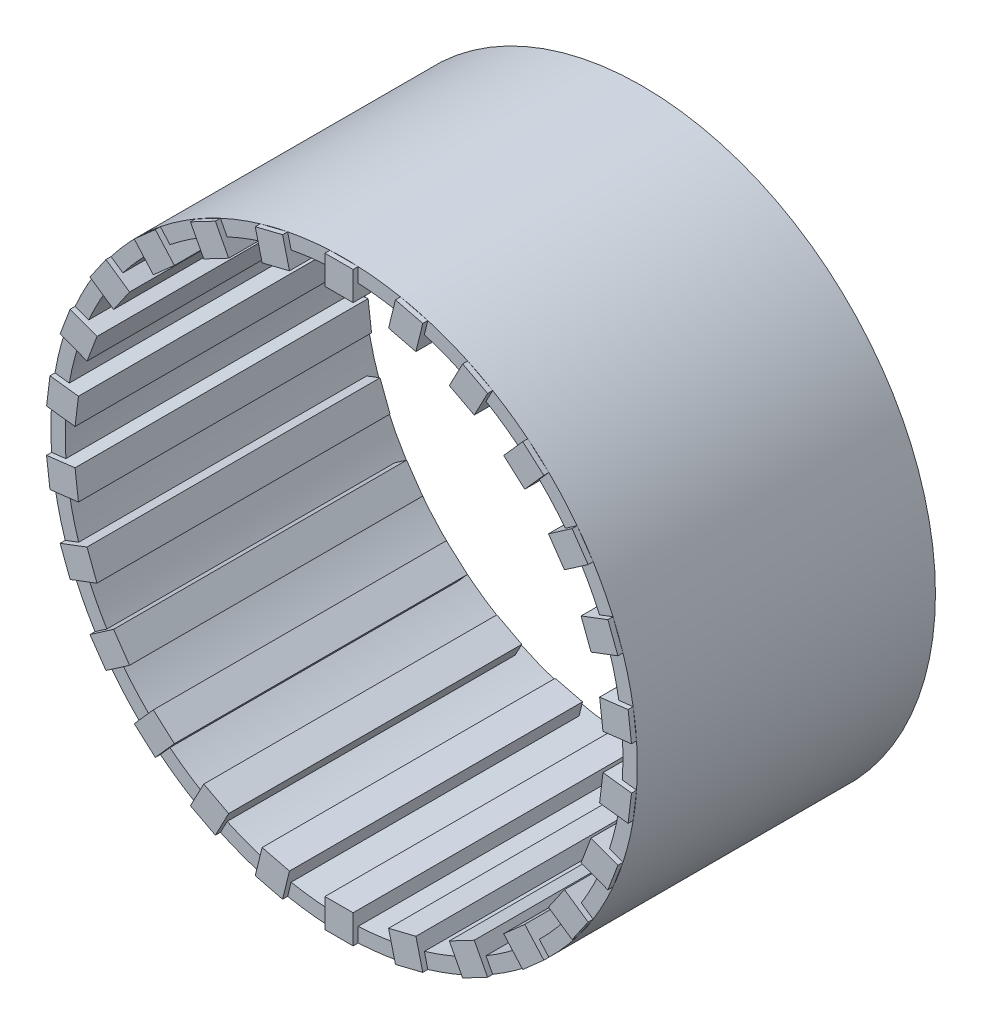
SolidWorks part; units mm, degrees
ref_plane "Front Plane" through (0, 0, 0) normal (0, 0, 1) x (1, 0, 0)
ref_plane "Top Plane" through (0, 0, 0) normal (0, 1, 0) x (1, 0, 0)
ref_plane "Right Plane" through (0, 0, 0) normal (1, 0, 0) x (0, 0, -1)
sketch "Sketch1" plane through (0, 0, 0) normal (0, 0, 1) x (1, 0, 0)
  circle A0 centre (0, 0) radius 14.0174
  circle A1 centre (0, 0) radius 14.7411
extrude "Boss-Extrude2" add sketch "Sketch1" along normal blind 14.986
sketch "Sketch2" plane through (0, 0, 14.986) normal (0, 0, 1) x (1, 0, 0)
  line L1 (0, 13.2804) -> (0.7077, 13.2804)
  line L2 (0.7077, 13.2804) -> (0.7077, 14.7241)
  line L3 (0.7077, 14.7241) -> (-0.7077, 14.7241)
  line L4 (-0.7077, 14.7241) -> (-0.7077, 13.2804)
  line L5 (-0.7077, 13.2804) -> (0, 13.2804)
  circle A0 centre (0, 0) radius 14.7411 construction
  point P5 (0, 0)
extrude "Boss-Extrude3" add sketch "Sketch2" against normal blind 14.478 and the other way blind 0.254
pattern_circular "CirPattern1" count 26 over 360 about axis through (0, 0, 0) along (0, 0, 1) of "Boss-Extrude3"
